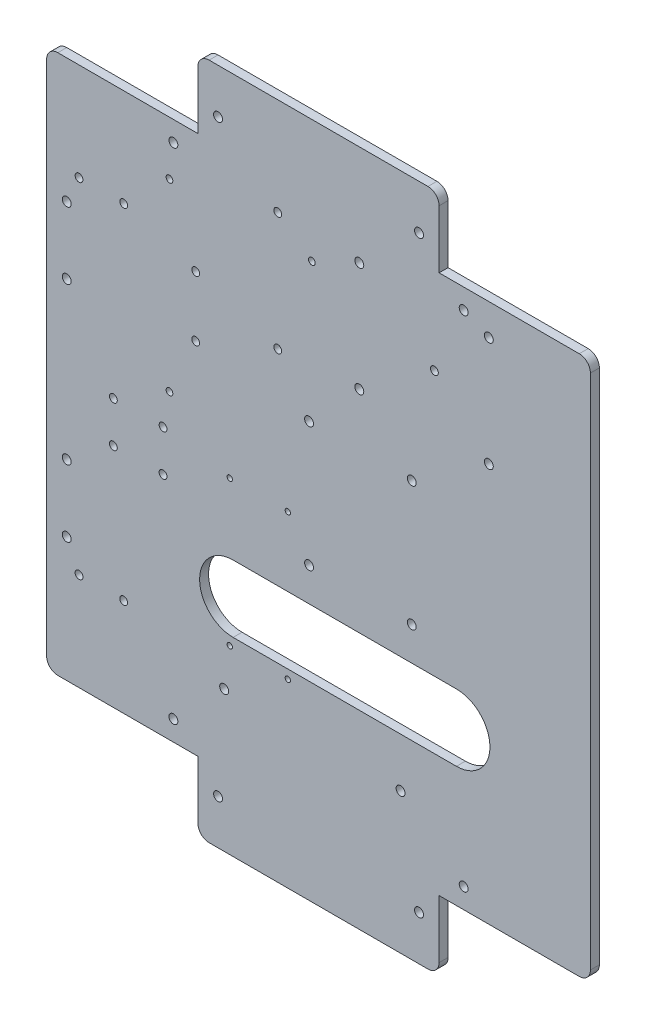
SolidWorks part; units mm, degrees
material "Alliage 1060"
ref_plane "Plan de dessus" through (0, 0, 0) normal (0, 0, 1) x (1, 0, 0)
ref_plane "Plan de droite" through (0, 0, 0) normal (0, 1, 0) x (1, 0, 0)
ref_plane "Plan de face" through (0, 0, 0) normal (1, 0, 0) x (0, 0, -1)
sketch "Esquisse1" plane through (0, 0, 0) normal (0, 0, 1) x (1, 0, 0)
  line L0 (0, 0) -> (-200, 0)
  line L1 (-200, 0) -> (-224.7487, 24.7487)
  line L2 (-224.7487, 24.7487) -> (-224.7487, 284.7487)
  line L3 (-224.7487, 284.7487) -> (-200, 309.4975)
  line L4 (-200, 309.4975) -> (0, 309.4975)
  line L5 (0, 309.4975) -> (24.7487, 284.7487)
  line L6 (24.7487, 284.7487) -> (24.7487, 24.7487)
  line L7 (24.7487, 24.7487) -> (0, 0)
  dimension "D1" = 260
  dimension "D2" = 35
  dimension "D3" = 135
  dimension "D4" = 200
extrude "Base" add sketch "Esquisse1" along normal blind 4
fillet "Congé1" radius 3 8 edges at (-200, 0, 2) (-224.7487, 24.7487, 2) (-224.7487, 284.7487, 2) (-200, 309.4975, 2) (0, 309.4975, 2) (24.7487, 284.7487, 2) (24.7487, 24.7487, 2) (0, 0, 2)
sketch "Esquisse19" plane through (0, 0, 0) normal (0, 0, -1) x (-1, 0, 0)
  line L0 (100, 309.4975) -> (100, 0) construction
  line L1 (1.2426, 309.4975) -> (198.7574, 309.4975) construction
  line L2 (198.7574, 0) -> (1.2426, 0) construction
  line L3 (-24.7487, 154.7487) -> (224.7487, 154.7487) construction
  line L4 (-24.7487, 25.9914) -> (-24.7487, 283.5061) construction
  line L5 (224.7487, 283.5061) -> (224.7487, 25.9914) construction
sketch "Esquisse25" plane through (0, 0, 0) normal (0, 0, -1) x (-1, 0, 0)
  line L0 (-24.7487, 25.9914) -> (-24.7487, 283.5061) construction
  line L1 (-21.7487, 33) -> (45, 33)
  line L2 (-24.7487, 33) -> (-24.7487, 0)
  line L3 (-24.7487, 0) -> (45, 0)
  line L4 (45, 33) -> (45, 3)
  line L5 (198.7574, 0) -> (1.2426, 0) construction
  line L6 (100, 309.4975) -> (100, 0) construction
  line L7 (100, 0) -> (100, 309.4975) construction
  line L8 (-24.7487, 154.7487) -> (224.7487, 154.7487) construction
  line L9 (224.7487, 0) -> (155, 0)
  line L10 (155, 33) -> (155, 3)
  line L11 (221.7487, 33) -> (155, 33)
  line L12 (224.7487, 33) -> (224.7487, 0)
  line L13 (224.7487, 276.4975) -> (224.7487, 309.4975)
  line L14 (221.7487, 276.4975) -> (155, 276.4975)
  line L15 (155, 276.4975) -> (155, 306.4975)
  line L16 (224.7487, 309.4975) -> (155, 309.4975)
  line L17 (-24.7487, 309.4975) -> (45, 309.4975)
  line L18 (45, 276.4975) -> (45, 306.4975)
  line L19 (-21.7487, 276.4975) -> (45, 276.4975)
  line L20 (-24.7487, 276.4975) -> (-24.7487, 309.4975)
  line L22 (45, 309.4975) -> (155, 309.4975)
  line L24 (45, 306.4975) -> (155, 306.4975)
  line L26 (45, 0) -> (155, 0)
  line L28 (45, 3) -> (155, 3)
  line L31 (-24.7487, 276.4975) -> (-24.7487, 33)
  line L33 (-21.7487, 276.4975) -> (-21.7487, 33)
  line L35 (224.7487, 276.4975) -> (224.7487, 33)
  line L37 (221.7487, 276.4975) -> (221.7487, 33)
  dimension "D1" = 55
  dimension "D2" = 33
  dimension "D3" = 3
  dimension "D4" = 3
  dimension "D5" = 3
  dimension "D6" = 3
extrude "Enlèv. mat.-Extru.1" cut sketch "Esquisse25" against normal through all
sketch "Esquisse33" plane through (0, 0, 4) normal (0, 0, 1) x (1, 0, 0)
  line L0 (-207.2487, 231.7487) -> (-187.2487, 231.7487) construction
  line L2 (-221.7487, 33) -> (-221.7487, 276.4975) construction
  line L3 (-221.7487, 154.7487) -> (21.7487, 154.7487) construction
  line L4 (21.7487, 276.4975) -> (21.7487, 33) construction
  line L5 (-100, 306.4975) -> (-100, 3) construction
  line L6 (-155, 306.4975) -> (-45, 306.4975) construction
  line L7 (-45, 3) -> (-155, 3) construction
  circle A0 centre (-207.2487, 231.7487) radius 1.75
  circle A1 centre (-187.2487, 231.7487) radius 1.75
  circle A2 centre (-207.2487, 77.7487) radius 1.75
  circle A3 centre (-187.2487, 77.7487) radius 1.75
  dimension "D3" = 3.5
  dimension "D1" = 20
  dimension "D2" = 14.5
  dimension "D4" = 77
extrude "Percage Main_De_Dieu" cut sketch "Esquisse33" against normal through all
sketch "Esquisse26" plane through (0, 0, 0) normal (0, 0, -1) x (-1, 0, 0)
  line L0 (212.7487, 189.7487) -> (212.7487, 219.7487) construction
  line L1 (221.7487, 33) -> (221.7487, 276.4975) construction
  line L2 (-24.7487, 154.7487) -> (224.7487, 154.7487) construction
  line L3 (224.7487, 154.7487) -> (-24.7487, 154.7487) construction
  line L4 (100, 309.4975) -> (100, 0) construction
  circle A0 centre (212.7487, 189.7487) radius 2
  circle A1 centre (212.7487, 219.7487) radius 2
  circle A2 centre (212.7487, 89.7487) radius 2
  circle A3 centre (212.7487, 119.7487) radius 2
  point P8 (212.7487, 204.7487)
  dimension "D1" = 4
  dimension "D2" = 30
  dimension "D3" = 9
  dimension "D4" = 50
extrude "Percage Buck Converter" cut sketch "Esquisse26" against normal through all
sketch "Esquisse27" plane through (0, 0, 0) normal (0, 0, -1) x (-1, 0, 0)
  line L0 (142.2513, 66) -> (63.2513, 66) construction
  line L1 (-21.7487, 276.4975) -> (-21.7487, 33) construction
  line L2 (-21.7487, 33) -> (45, 33) construction
  circle A0 centre (142.2513, 66) radius 2
  circle A1 centre (63.2513, 66) radius 2
  dimension "D2" = 4
  dimension "D1" = 79
  dimension "D3" = 85
  dimension "D4" = 33
extrude "Percage Teensy Moteur" cut sketch "Esquisse27" against normal through all
sketch "Esquisse28" plane through (0, 0, 0) normal (0, 0, -1) x (-1, 0, 0)
  line L0 (166.7487, 169.0225) -> (166.7487, 251.4975) construction
  line L1 (166.7487, 251.4975) -> (102.9987, 251.4975) construction
  line L2 (224.7487, 154.7487) -> (-24.7487, 154.7487) construction
  line L3 (221.7487, 33) -> (221.7487, 276.4975) construction
  line L4 (221.7487, 276.4975) -> (155, 276.4975) construction
  circle A0 centre (166.7487, 251.4975) radius 1.5
  circle A1 centre (102.9987, 251.4975) radius 1.5
  circle A2 centre (166.7487, 169.0225) radius 1.5
  dimension "D1" = 3
  dimension "D2" = 63.75
  dimension "D3" = 82.475
  dimension "D4" = 55
  dimension "D5" = 25
extrude "Percage Carte Alim" cut sketch "Esquisse28" against normal through all
sketch "Esquisse29" plane through (0, 0, 0) normal (0, 0, -1) x (-1, 0, 0)
  line L0 (221.7487, 33) -> (221.7487, 276.4975) construction
  line L1 (81.7487, 212.4975) -> (23.7487, 212.4975) construction
  line L2 (81.7487, 212.4975) -> (81.7487, 261.4975) construction
  line L3 (81.7487, 261.4975) -> (23.7487, 261.4975) construction
  line L4 (23.7487, 212.4975) -> (23.7487, 261.4975) construction
  line L5 (221.7487, 276.4975) -> (155, 276.4975) construction
  circle A0 centre (81.7487, 212.4975) radius 2
  circle A1 centre (23.7487, 212.4975) radius 2
  circle A2 centre (23.7487, 261.4975) radius 2
  circle A3 centre (81.7487, 261.4975) radius 2
  dimension "D3" = 4
  dimension "D1" = 49
  dimension "D2" = 58
  dimension "D4" = 140
  dimension "D5" = 15
extrude "Percage Rasp" cut sketch "Esquisse29" against normal through all
sketch "Esquisse32" plane through (0, 0, 4) normal (0, 0, 1) x (1, 0, 0)
  line L0 (-118.2513, 262.8275) -> (-118.2513, 209.8275) construction
  line L1 (-48.1113, 236.4975) -> (-118.2513, 236.4975) construction
  line L2 (-45, 276.4975) -> (21.7487, 276.4975) construction
  line L3 (21.7487, 276.4975) -> (21.7487, 33) construction
  circle A0 centre (-118.2513, 262.8275) radius 1.75
  circle A1 centre (-118.2513, 209.8275) radius 1.75
  circle A2 centre (-48.1113, 236.4975) radius 1.75
  dimension "D1" = 3.5
  dimension "D2" = 53
  dimension "D3" = 70.14
  dimension "D4" = 26.33
  dimension "D5" = 40
  dimension "D6" = 140
extrude "Percage Teensy Actionneurs" cut sketch "Esquisse32" against normal through all
sketch "Esquisse30" plane through (0, 0, 0) normal (0, 0, -1) x (-1, 0, 0)
  line L0 (-21.7487, 276.4975) -> (-21.7487, 33) construction
  line L1 (104.2513, 133) -> (58.2513, 133) construction
  line L2 (104.2513, 133) -> (104.2513, 188.8) construction
  line L3 (104.2513, 188.8) -> (58.2513, 188.8) construction
  line L4 (58.2513, 133) -> (58.2513, 188.8) construction
  line L5 (-21.7487, 33) -> (45, 33) construction
  circle A0 centre (104.2513, 133) radius 2
  circle A1 centre (58.2513, 133) radius 2
  circle A2 centre (58.2513, 188.8) radius 2
  circle A3 centre (104.2513, 188.8) radius 2
  dimension "D3" = 4
  dimension "D1" = 55.8
  dimension "D2" = 46
  dimension "D4" = 80
  dimension "D5" = 100
extrude "Percage Alim Actionneurs" cut sketch "Esquisse30" against normal through all
sketch "Esquisse31" plane through (0, 0, 0) normal (0, 0, -1) x (-1, 0, 0)
  line L0 (138.2513, 103) -> (38.2513, 103) construction
  line L1 (138.2513, 88) -> (38.2513, 88)
  line L2 (138.2513, 118) -> (38.2513, 118)
  line L3 (-21.7487, 33) -> (45, 33) construction
  line L4 (-21.7487, 276.4975) -> (-21.7487, 33) construction
  arc A0 (138.2513, 88) -> (138.2513, 118) centre (138.2513, 103) ccw
  arc A1 (38.2513, 118) -> (38.2513, 88) centre (38.2513, 103) ccw
  point P2 (88.2513, 103)
  dimension "D2" = 15
  dimension "D1" = 100
  dimension "D3" = 70
  dimension "D4" = 60
extrude "Perçage Fils" cut sketch "Esquisse31" against normal through all
sketch "Esquisse34" plane through (0, 0, 0) normal (0, 0, -1) x (-1, 0, 0)
  line L0 (221.7487, 154.7487) -> (-21.7487, 154.7487) construction
  line L1 (221.7487, 33) -> (221.7487, 276.4975) construction
  line L2 (-21.7487, 276.4975) -> (-21.7487, 33) construction
  line L3 (191.8737, 153.9) -> (169.6237, 153.9) construction
  line L4 (169.6237, 135.5) -> (191.8737, 135.5) construction
  line L5 (100, 306.4975) -> (100, 3) construction
  line L6 (155, 306.4975) -> (45, 306.4975) construction
  line L7 (45, 3) -> (155, 3) construction
  line L8 (155, 33) -> (221.7487, 33) construction
  circle A2 centre (169.6237, 153.9) radius 1.75
  circle A3 centre (191.8737, 153.9) radius 1.75
  circle A4 centre (169.6237, 135.5) radius 1.75
  circle A5 centre (191.8737, 135.5) radius 1.75
  point P12 (180.7487, 153.9)
  dimension "D2" = 3.5
  dimension "D5" = 102.5
  dimension "D3" = 22.25
  dimension "D4" = 41
  dimension "D7" = 18.4
extrude "Perçage Moteur Ascenseur" cut sketch "Esquisse34" against normal through all
sketch "Esquisse35" plane through (0, 0, 4) normal (0, 0, 1) x (1, 0, 0)
  line L0 (-155, 33) -> (-221.7487, 33) construction
  line L1 (-139.7487, 149) -> (-113.7487, 149) construction
  line L2 (-139.7487, 149) -> (-139.7487, 84) construction
  line L3 (-139.7487, 84) -> (-113.7487, 84) construction
  line L4 (-113.7487, 149) -> (-113.7487, 84) construction
  line L5 (-221.7487, 33) -> (-221.7487, 276.4975) construction
  circle A0 centre (-139.7487, 149) radius 1.2
  circle A1 centre (-113.7487, 149) radius 1.2
  circle A2 centre (-113.7487, 84) radius 1.2
  circle A3 centre (-139.7487, 84) radius 1.2
  dimension "D3" = 2.4
  dimension "D1" = 26
  dimension "D2" = 65
  dimension "D4" = 51
  dimension "80" = 82
extrude "Perçage Driver Ascenseur" cut sketch "Esquisse35" against normal through all
sketch "Esquisse36" plane through (0, 0, 4) normal (0, 0, 1) x (1, 0, 0)
  line L0 (-155, 33) -> (-155, 144.3181) construction
  line L2 (-221.7487, 276.4975) -> (-155, 276.4975) construction
  circle A0 centre (-155, 194.4975) radius 1.75
  circle A1 centre (-155, 221.4975) radius 1.75
  dimension "D3" = 3.5
  dimension "D1" = 27
  dimension "D2" = 55
extrude "Enlèv. mat.-Extru.2" cut sketch "Esquisse36" against normal blind 5
sketch "Esquisse39" plane through (0, 0, 4) normal (0, 0, 1) x (1, 0, 0)
  line L0 (-100, 306.4975) -> (-100, 3) construction
  line L1 (-155, 276.4975) -> (-145, 276.4975) construction
  line L2 (-155, 276.4975) -> (-155, 286.4975) construction
  line L3 (-155, 286.4975) -> (-145, 286.4975) construction
  line L4 (-145, 276.4975) -> (-145, 286.4975) construction
  line L5 (-155, 276.4975) -> (-165, 276.4975) construction
  line L6 (-155, 276.4975) -> (-155, 266.4975) construction
  line L7 (-155, 266.4975) -> (-165, 266.4975) construction
  line L8 (-165, 276.4975) -> (-165, 266.4975) construction
  line L9 (-155, 306.4975) -> (-45, 306.4975) construction
  line L10 (-45, 3) -> (-155, 3) construction
  line L11 (-221.7487, 154.7487) -> (21.7487, 154.7487) construction
  line L12 (-221.7487, 33) -> (-221.7487, 276.4975) construction
  line L13 (21.7487, 276.4975) -> (21.7487, 33) construction
  circle A0 centre (-145, 286.4975) radius 2
  circle A1 centre (-165, 266.4975) radius 2
  circle A2 centre (-35, 266.4975) radius 2
  circle A3 centre (-55, 286.4975) radius 2
  circle A4 centre (-35, 43) radius 2
  circle A5 centre (-55, 23) radius 2
  circle A6 centre (-165, 43) radius 2
  circle A7 centre (-145, 23) radius 2
  dimension "D3" = 4
  dimension "D1" = 10
  dimension "D2" = 10
extrude "Perçage Equerre" cut sketch "Esquisse39" against normal through all
sketch "Esquisse38" plane through (0, 0, 0) normal (0, 0, -1) x (-1, 0, 0)
  line L0 (-21.7487, 33) -> (45, 33) construction
  line L1 (-21.7487, 3) -> (46, 3)
  line L2 (-21.7487, 3) -> (-21.7487, 34)
  line L3 (-21.7487, 34) -> (46, 34)
  line L4 (46, 3) -> (46, 34)
  line L5 (45, 33) -> (45, 3) construction
  line L6 (45, 3) -> (155, 3) construction
  line L7 (-21.7487, 276.4975) -> (-21.7487, 33) construction
  line L8 (221.7487, 33) -> (221.7487, 276.4975) construction
  line L9 (221.7487, 3) -> (154, 3)
  line L10 (221.7487, 3) -> (221.7487, 34)
  line L11 (221.7487, 34) -> (154, 34)
  line L12 (154, 3) -> (154, 34)
  line L15 (155, 306.4975) -> (45, 306.4975) construction
  line L16 (221.7487, 306.4975) -> (154, 306.4975)
  line L17 (221.7487, 306.4975) -> (221.7487, 275.4975)
  line L18 (221.7487, 275.4975) -> (154, 275.4975)
  line L19 (154, 306.4975) -> (154, 275.4975)
  line L20 (-21.7487, 306.4975) -> (46, 306.4975)
  line L21 (-21.7487, 306.4975) -> (-21.7487, 275.4975)
  line L22 (-21.7487, 275.4975) -> (46, 275.4975)
  line L23 (46, 306.4975) -> (46, 275.4975)
  dimension "D1" = 1
  dimension "D2" = 1
extrude "Enlèv. mat.-Extru.3" cut sketch "Esquisse38" against normal through all
fillet "Congé2" radius 5 8 edges at (-221.7487, 275.4975, 2) (-154, 306.4975, 2) (-46, 306.4975, 2) (21.7487, 275.4975, 2) (-221.7487, 34, 2) (-154, 3, 2) (-46, 3, 2) (21.7487, 34, 2)
